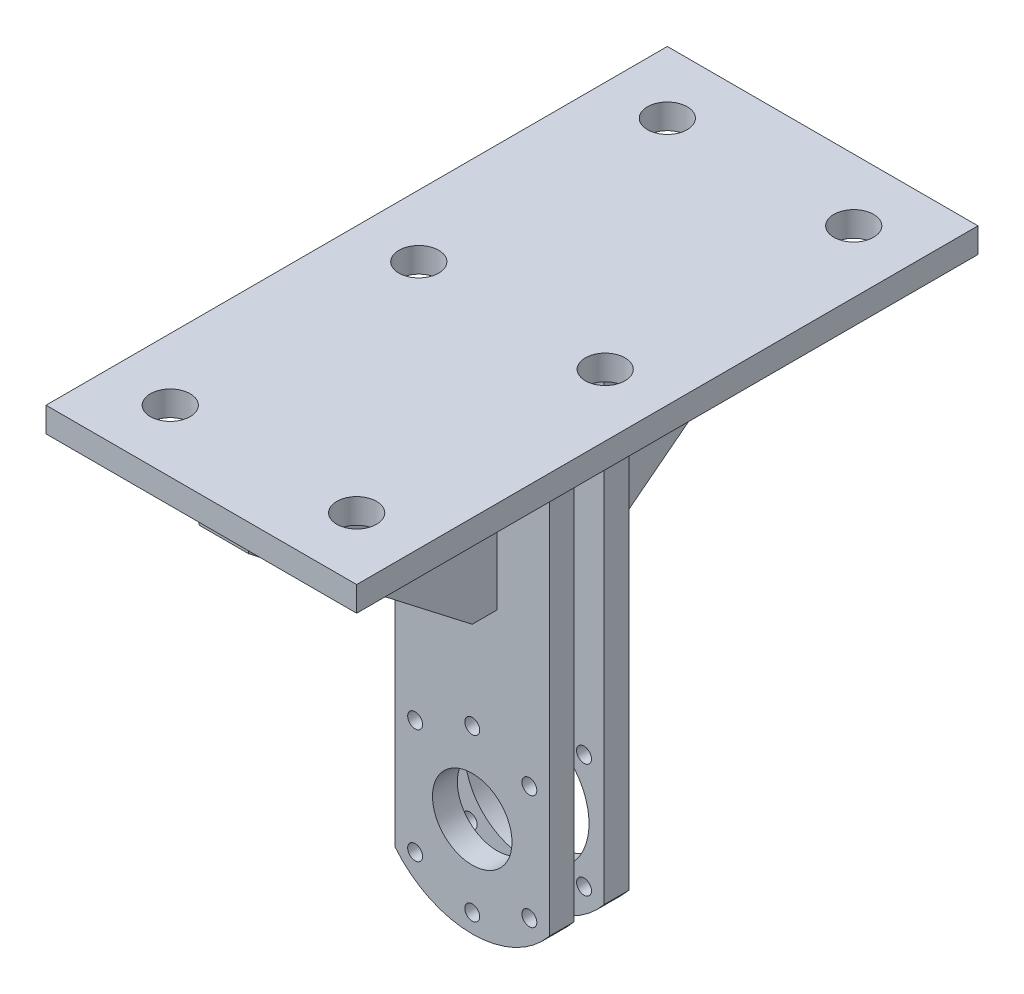
SolidWorks part; units mm, degrees
ref_plane "Front Plane" through (0, 0, 0) normal (0, 0, 1) x (1, 0, 0)
ref_plane "Top Plane" through (0, 0, 0) normal (0, 1, 0) x (1, 0, 0)
ref_plane "Right Plane" through (0, 0, 0) normal (1, 0, 0) x (0, 0, -1)
sketch "Sketch1" plane through (0, 0, 0) normal (0, 0, 1) x (1, 0, 0)
  line L0 (-31, -25.2784) -> (-31, 157.5216)
  line L3 (31, -25.2784) -> (31, 157.5216)
  line L4 (-31, 157.5216) -> (31, 157.5216)
  arc A3 (-31, -25.2784) -> (31, -25.2784) centre (0, 0) ccw
  circle A5 centre (0, 32.5) radius 3
  circle A6 centre (-22.981, 22.981) radius 3
  circle A7 centre (22.981, 22.981) radius 3
  circle A8 centre (22.981, -22.981) radius 3
  circle A9 centre (0, -32.5) radius 3
  circle A10 centre (-22.981, -22.981) radius 3
  circle A12 centre (0, 0) radius 16
  point P4 (0, 0)
  dimension "D4" = 80
  dimension "D6" = 6
  dimension "D9" = 6
  dimension "D10" = 6
  dimension "D3" = 32
  dimension "D2" = 182.8
extrude "Boss-Extrude1" add sketch "Sketch1" along normal blind 10
ref_plane "Plane1" through (0, 0, -12) normal (0, 0, -1) x (-1, 0, 0)
sketch "Sketch2" plane through (0, 0, -12) normal (0, 0, -1) x (-1, 0, 0)
  line L0 (-31, 157.5216) -> (31, 157.5216)
  line L1 (31, 157.5216) -> (31, -25.2784)
  line L2 (-31, 157.5216) -> (-31, -25.2784)
  arc A0 (-31, -25.2784) -> (31, -25.2784) centre (0, 0) ccw
  circle A1 centre (0, 32.5) radius 3.0369
  circle A2 centre (22.981, 22.981) radius 3
  circle A3 centre (-22.981, 22.981) radius 3
  circle A4 centre (22.981, -22.981) radius 3
  circle A5 centre (0, -32.5) radius 3
  circle A6 centre (-22.981, -22.981) radius 3
  circle A7 centre (0, 0) radius 25
  dimension "D1" = 50
extrude "Boss-Extrude2" add sketch "Sketch2" along normal blind 10 separate body
sketch "Sketch3" plane through (0, 157.5216, 0) normal (0, 1, 0) x (1, 0, 0)
  line L4 (-62.5, -119) -> (62.5, -119)
  line L5 (-62.5, -119) -> (-62.5, 131)
  line L6 (-62.5, 131) -> (62.5, 131)
  line L7 (62.5, -119) -> (62.5, 131)
  line L8 (-62.5, -119) -> (62.5, 131) construction
  line L9 (-62.5, 131) -> (62.5, -119) construction
  point P6 (0, 6)
  dimension "D1" = 250
  dimension "D2" = 125
extrude "Boss-Extrude3" add sketch "Sketch3" along normal blind 10
sketch "Sketch5" plane through (0, 0, 0) normal (1, 0, 0) x (0, 0, -1)
  line L0 (22, 157.5216) -> (122, 157.5216)
  line L1 (-119, 157.5216) -> (131, 157.5216) construction
  line L2 (122, 157.5216) -> (122, 147.5216)
  line L3 (122, 147.5216) -> (32, 77.9333)
  line L4 (32, 77.9333) -> (22, 77.9333)
  line L5 (22, 157.5216) -> (22, -25.2784) construction
  line L6 (22, 77.9333) -> (22, 157.5216)
  line L8 (-20, 77.9333) -> (-10, 77.9333)
  line L9 (-110, 147.5216) -> (-20, 77.9333)
  line L10 (-110, 157.5216) -> (-110, 147.5216)
  line L11 (-10, 157.5216) -> (-110, 157.5216)
  line L12 (-10, 77.9333) -> (-10, 157.5216)
  dimension "D1" = 100
  dimension "D2" = 10
  dimension "D3" = 10
extrude "Boss-Extrude4" add sketch "Sketch5" along normal mid plane 20
sketch "Sketch6" plane through (0, 167.5216, 0) normal (0, 1, 0) x (1, 0, 0)
  circle A0 centre (-37.5, 106) radius 8
  circle A1 centre (37.5, 106) radius 8
  circle A2 centre (37.5, 6) radius 8
  circle A3 centre (37.5, -94) radius 8
  circle A4 centre (-37.5, -94) radius 8
  circle A5 centre (-37.5, 6) radius 8
  dimension "D2" = 16
extrude "Cut-Extrude1" cut sketch "Sketch6" against normal blind 10
